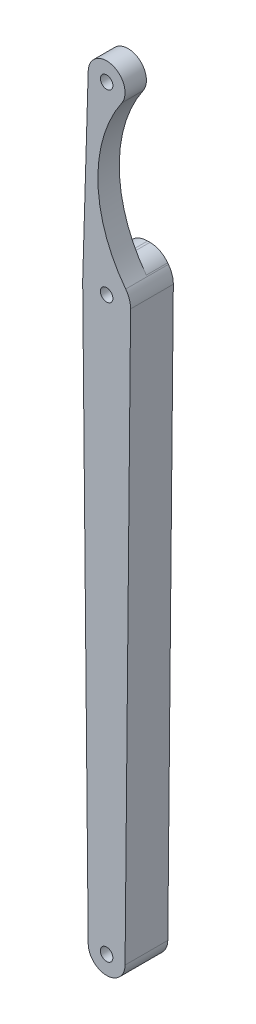
SolidWorks part; units mm, degrees
ref_plane "前视基准面" through (0, 0, 0) normal (0, 0, 1) x (1, 0, 0)
ref_plane "上视基准面" through (0, 0, 0) normal (0, 1, 0) x (1, 0, 0)
ref_plane "右视基准面" through (0, 0, 0) normal (1, 0, 0) x (0, 0, -1)
sketch "草图1" plane through (0, 0, 0) normal (0, 0, 1) x (1, 0, 0)
  line L0 (-174.6627, -131) -> (-174.6627, 24) construction
  line L1 (-174.6627, 24) -> (-174.6627, 74) construction
  line L2 (-181.1624, 23.9371) -> (-179.6625, -131.0484)
  line L3 (-181.1598, 24.195) -> (-179.6604, 74.15)
  line L4 (-169.6629, -131.0484) -> (-168.163, 23.9371)
  circle A0 centre (-174.6627, 24) radius 1.7
  arc A1 (-168.163, 23.9371) -> (-169.4935, 27.9407) centre (-174.6627, 24) ccw
  arc A2 (-179.6625, -131.0484) -> (-169.6629, -131.0484) centre (-174.6627, -131) ccw
  arc A3 (-170.5438, 71.1654) -> (-179.6604, 74.15) centre (-174.6627, 74) ccw
  arc A4 (-169.4935, 27.9407) -> (-170.5438, 71.1654) centre (-140.1925, 50.2778) cw
  arc A5 (-181.1598, 24.195) -> (-181.1624, 23.9371) centre (-174.6627, 24) ccw
  circle A6 centre (-174.6627, -131) radius 1.7
  circle A7 centre (-174.6627, 74) radius 1.7
  dimension "D1" = 155
  dimension "D2" = 10
  dimension "D3" = 13
  dimension "D4" = 10
  dimension "D5" = 50
extrude "凸台-拉伸1" add sketch "草图1" along normal mid plane 11.6
sketch "草图2" plane through (0, 0, 0) normal (1, 0, 0) x (0, 0, -1)
  line L0 (0, 24) -> (0, 74) construction
  line L1 (5.8, 79) -> (0, 79)
  line L2 (5.8, 79) -> (5.8, 30.6125)
  line L3 (5.8, 30.6125) -> (0, 30.6125)
  line L4 (0, 79) -> (0, 30.6125)
extrude "切除-拉伸1" cut sketch "草图2" against normal blind 279.6
fillet "圆角1" radius 6 2 edges at (-171.3496, 30.6125, -2.9) (-180.9672, 30.6125, -2.9)
